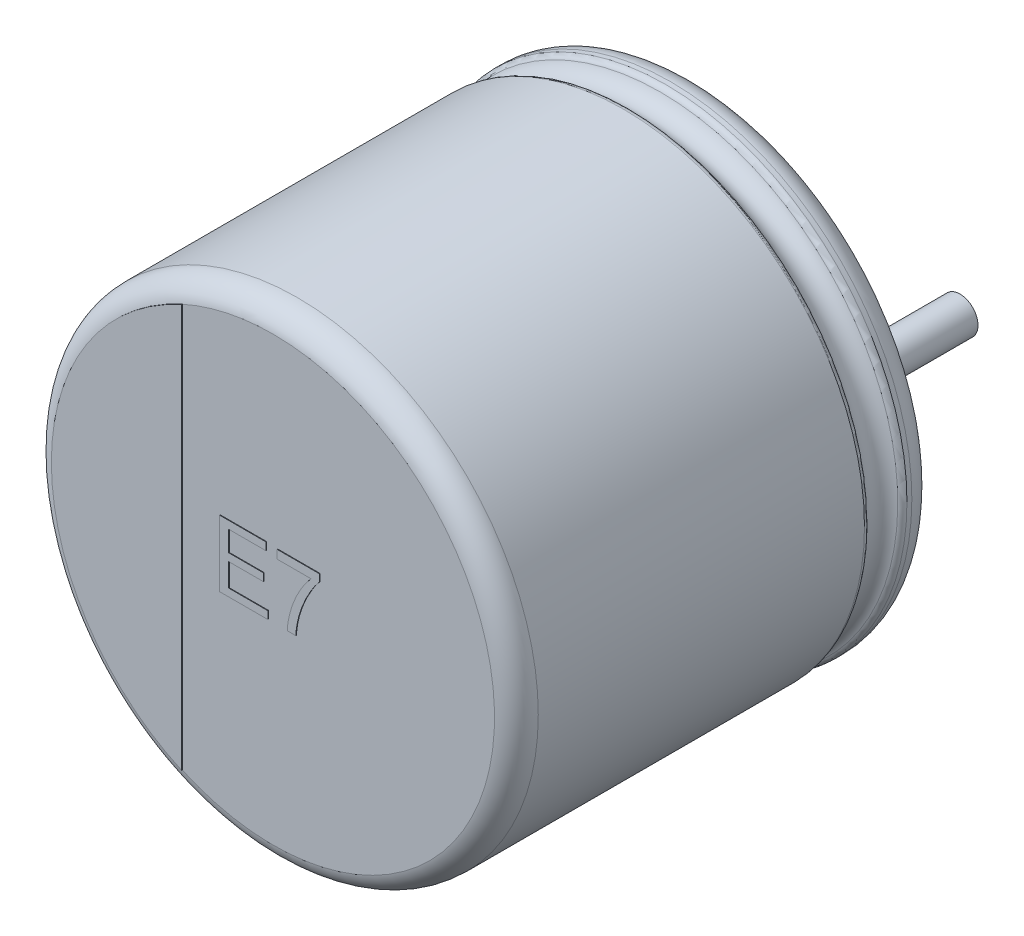
SolidWorks part; units mm, degrees
ref_plane "Plan de face" through (0, 0, 0) normal (0, 0, 1) x (1, 0, 0)
ref_plane "Plan de dessus" through (0, 0, 0) normal (0, 1, 0) x (1, 0, 0)
ref_plane "Plan de droite" through (0, 0, 0) normal (1, 0, 0) x (0, 0, -1)
sketch "Sketch10" plane through (0, 0, 0) normal (1, 0, 0) x (0, 0, -1)
  line L0 (18.1631, 0) -> (-18.9631, 0) construction
  line L1 (-7, 0) -> (-0.05, 0)
  line L2 (-7, 0) -> (-7, 3.6736)
  line L3 (-6.6, 4) -> (-1.1846, 4)
  line L4 (-0.05, 3.4031) -> (-0.05, 0)
  line L7 (-0.4794, 4) -> (-0.3982, 4)
  arc A0 (-7, 3.6736) -> (-6.6, 4) centre (-6.6068, 3.6001) cw
  arc A1 (-0.3982, 4) -> (-0.05, 3.4031) centre (-0.3982, 3.6) cw
  arc A2 (-0.5713, 3.9394) -> (-1.0926, 3.9394) centre (-0.832, 4.051) cw
  arc A3 (-1.0926, 3.9394) -> (-1.1846, 4) centre (-1.1846, 3.9) ccw
  arc A4 (-0.5713, 3.9394) -> (-0.4794, 4) centre (-0.4794, 3.9) cw
  point P4 (0.57, 0)
  point P13 (-7, 4)
  dimension "D2" = 0.4
  dimension "D3" = 0.4
  dimension "D4" = 0.1
  dimension "D5" = 0.1
  dimension "D1" = 4
revolve "Повернуть1" add sketch "Sketch10" angle 360 about L0
sketch "Эскиз2" plane through (0, 0, 0.05) normal (0, 0, -1) x (-1, 0, 0)
  line L1 (0, 0.7993) -> (0, -1.0496) construction
  line L2 (-1.75, 0) -> (3.1313, 0) construction
  circle A3 centre (-1.75, 0) radius 0.3
  circle A7 centre (1.75, 0) radius 0.3
  dimension "D1" = 3.5
extrude "Бобышка-Вытянуть1" add sketch "Эскиз2" along normal blind 2.7
sketch "Эскиз4" plane through (0, 0, 7) normal (0, 0, 1) x (1, 0, 0)
  line L0 (-1.5096, -3.3491) -> (-1.5096, 3.3491)
  circle A1 centre (0, 0) radius 3.6736 construction
  arc A2 (-1.5096, 3.3491) -> (-1.5096, -3.3491) centre (0, 0) ccw
extrude "Бобышка-Вытянуть2" add sketch "Эскиз4" along normal blind 0.01
sketch "Эскиз5" plane through (0, 0, 7) normal (0, 0, 1) x (1, 0, 0)
  text T0 "E7" font "Arial" height 1.1
extrude "Текст" add sketch "Эскиз5" along normal blind 0.01
sketch "Эскиз6" plane through (0, 0, 0.05) normal (0, 0, -1) x (-1, 0, 0)
  line L0 (-1.75, 0.4656) -> (-2.1332, 0.4656)
  line L1 (-1.75, -0.4656) -> (-2.1332, -0.4656)
  line L2 (1.75, -0.4656) -> (2.1332, -0.4656)
  line L3 (1.75, 0.4656) -> (2.1332, 0.4656)
  arc A0 (-2.3702, -0.7952) -> (2.3702, -0.7952) centre (0, 0) ccw
  arc A1 (-1.75, -0.4656) -> (-1.75, 0.4656) centre (-1.75, 0) ccw
  arc A2 (1.75, 0.4656) -> (1.75, -0.4656) centre (1.75, 0) ccw
  arc A3 (2.3702, 0.7952) -> (-2.3702, 0.7952) centre (0, 0) ccw
  arc A4 (2.1332, 0.4656) -> (2.3702, 0.7952) centre (2.1332, 0.7156) ccw
  arc A5 (2.1332, -0.4656) -> (2.3702, -0.7952) centre (2.1332, -0.7156) cw
  arc A6 (-2.3702, -0.7952) -> (-2.1332, -0.4656) centre (-2.1332, -0.7156) cw
  arc A7 (-2.1332, 0.4656) -> (-2.3702, 0.7952) centre (-2.1332, 0.7156) cw
  point P7 (2.4563, 0.4656)
  point P23 (0, -2.5)
  point P24 (0, 2.5)
  dimension "D1" = 0.25
  dimension "D2" = 5
extrude "Бобышка-Вытянуть5" add sketch "Эскиз6" along normal blind 0.05 contours A3 A7 L0 A1 L1 A6 A0 A5 L2 A2 L3 A4
